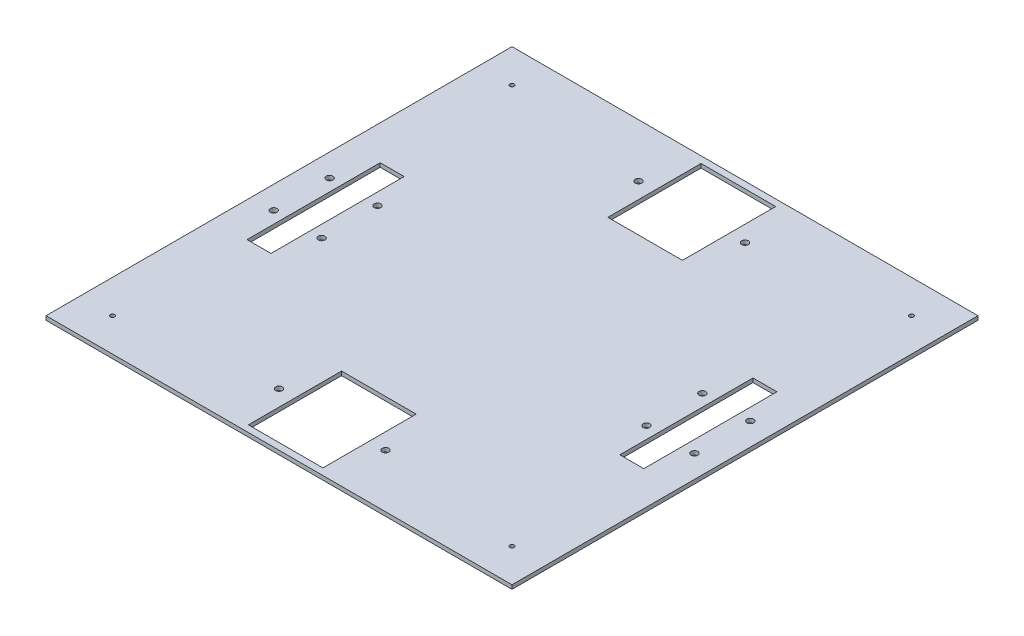
SolidWorks part; units mm, degrees
ref_plane "Front Plane" through (0, 0, 0) normal (0, 0, 1) x (1, 0, 0)
ref_plane "Top Plane" through (0, 0, 0) normal (0, 1, 0) x (1, 0, 0)
ref_plane "Right Plane" through (0, 0, 0) normal (1, 0, 0) x (0, 0, -1)
sketch "Sketch1" plane through (0, 0, 0) normal (0, 1, 0) x (1, 0, 0)
  line L1 (-175, 175) -> (175, 175)
  line L2 (-175, 175) -> (-175, -175)
  line L3 (-175, -175) -> (175, -175)
  line L4 (175, 175) -> (175, -175)
  line L5 (-175, 175) -> (175, -175) construction
  line L6 (-175, -175) -> (175, 175) construction
  point P0 (0, 0)
  dimension "D1" = 350
  dimension "D2" = 350
extrude "Boss-Extrude1" add sketch "Sketch1" along normal blind 3
sketch "Sketch3" plane through (0, 3, 0) normal (0, 1, 0) x (1, 0, 0)
  line L0 (-140, 0) -> (-140, -175) construction
  line L1 (-149, 50) -> (-131, 50)
  line L2 (-149, 50) -> (-149, -50)
  line L3 (-149, -50) -> (-131, -50)
  line L4 (-131, 50) -> (-131, -50)
  line L5 (-149, 50) -> (-131, -50) construction
  line L6 (-149, -50) -> (-131, 50) construction
  line L7 (131, 50) -> (149, 50)
  line L8 (131, 50) -> (131, -50)
  line L9 (131, -50) -> (149, -50)
  line L10 (149, 50) -> (149, -50)
  line L11 (131, 50) -> (149, -50) construction
  line L12 (131, -50) -> (149, 50) construction
  line L14 (-175, -175) -> (175, -175) construction
  line L15 (-140, 0) -> (-175, 0) construction
  line L17 (-175, 175) -> (-175, -175) construction
  line L18 (140, 0) -> (175, 0) construction
  line L19 (175, -175) -> (175, 175) construction
  line L20 (140, 0) -> (140, -175) construction
  point P0 (-140, 0)
  point P5 (140, 0)
extrude "Cut-Extrude1" cut sketch "Sketch3" against normal blind 3
sketch "Sketch4" plane through (0, 3, 0) normal (0, 1, 0) x (1, 0, 0)
  line L0 (0, 135) -> (0, 175) construction
  line L1 (-28, 170) -> (28, 170)
  line L2 (-28, 170) -> (-28, 100)
  line L3 (-28, 100) -> (28, 100)
  line L4 (28, 170) -> (28, 100)
  line L5 (-28, 170) -> (28, 100) construction
  line L6 (-28, 100) -> (28, 170) construction
  line L7 (-28, -100) -> (28, -100)
  line L8 (-28, -100) -> (-28, -170)
  line L9 (-28, -170) -> (28, -170)
  line L10 (28, -100) -> (28, -170)
  line L11 (-28, -100) -> (28, -170) construction
  line L12 (-28, -170) -> (28, -100) construction
  line L13 (175, 175) -> (-175, 175) construction
  line L14 (0, -135) -> (0, -175) construction
  line L15 (-175, -175) -> (175, -175) construction
  line L16 (0, 135) -> (175, 135) construction
  line L17 (175, -175) -> (175, 175) construction
  line L18 (0, 135) -> (-175, 135) construction
  line L19 (-175, 175) -> (-175, -175) construction
  line L20 (0, -135) -> (175, -135) construction
  line L21 (0, -135) -> (-175, -135) construction
  point P0 (0, 135)
  point P5 (0, -135)
extrude "Cut-Extrude2" cut sketch "Sketch4" against normal blind 3
sketch "Sketch5" plane through (0, 3, 0) normal (0, 1, 0) x (1, 0, 0)
  line L0 (-40, 135) -> (40, 135) construction
  line L1 (-158, 21) -> (-158, -21) construction
  line L2 (-158, -21) -> (-122, -21) construction
  line L3 (122, 21) -> (122, -21) construction
  line L4 (122, -21) -> (158, -21) construction
  line L5 (-158, 21) -> (-149, 21) construction
  line L6 (-40, -135) -> (40, -135) construction
  line L7 (-149, 50) -> (-149, -50) construction
  line L8 (-40, 135) -> (0, 170) construction
  line L9 (-122, 21) -> (-122, -21) construction
  line L10 (-122, 21) -> (-131, 21) construction
  line L11 (28, 170) -> (-28, 170) construction
  line L12 (-131, -50) -> (-131, 50) construction
  line L13 (0, 170) -> (40, 135) construction
  line L14 (158, 21) -> (158, -21) construction
  line L15 (122, 21) -> (131, 21) construction
  line L16 (131, 50) -> (131, -50) construction
  line L17 (158, 21) -> (149, 21) construction
  line L18 (149, -50) -> (149, 50) construction
  line L19 (40, 135) -> (0, 100) construction
  line L20 (-28, 100) -> (28, 100) construction
  line L21 (0, 100) -> (-40, 135) construction
  line L22 (-40, -135) -> (0, -100) construction
  line L23 (28, -100) -> (-28, -100) construction
  line L24 (0, -100) -> (40, -135) construction
  line L25 (40, -135) -> (0, -170) construction
  line L26 (-28, -170) -> (28, -170) construction
  line L27 (0, -170) -> (-40, -135) construction
  circle A0 centre (-158, 21) radius 2.5
  circle A1 centre (-158, -21) radius 2.5
  circle A2 centre (-122, 21) radius 2.5
  circle A3 centre (-122, -21) radius 2.5
  circle A4 centre (158, 21) radius 2.5
  circle A5 centre (158, -21) radius 2.5
  circle A6 centre (122, 21) radius 2.5
  circle A7 centre (122, -21) radius 2.5
  circle A8 centre (-40, -135) radius 2.5
  circle A9 centre (40, -135) radius 2.5
  circle A10 centre (-40, 135) radius 2.5
  circle A11 centre (40, 135) radius 2.5
  circle A12 centre (-150, 150) radius 1.6
  circle A13 centre (150, 150) radius 1.6
  circle A14 centre (150, -150) radius 1.6
  circle A15 centre (-150, -150) radius 1.6
extrude "Cut-Extrude3" cut sketch "Sketch5" against normal blind 3
